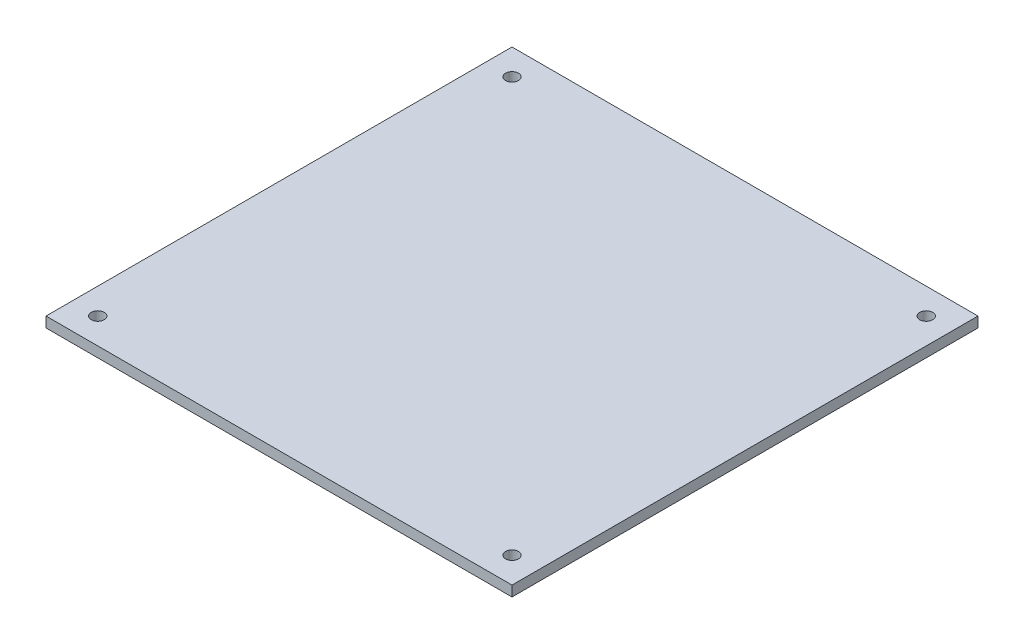
SolidWorks part; units mm, degrees
ref_plane "Front Plane" through (0, 0, 0) normal (0, 0, 1) x (1, 0, 0)
ref_plane "Top Plane" through (0, 0, 0) normal (0, 1, 0) x (1, 0, 0)
ref_plane "Right Plane" through (0, 0, 0) normal (1, 0, 0) x (0, 0, -1)
sketch "Sketch1" plane through (0, 0, 0) normal (0, 1, 0) x (1, 0, 0)
  line L1 (-45, -45) -> (45, -45)
  line L2 (-45, -45) -> (-45, 45)
  line L3 (-45, 45) -> (45, 45)
  line L4 (45, -45) -> (45, 45)
  line L5 (-45, -45) -> (45, 45) construction
  line L6 (-45, 45) -> (45, -45) construction
  point P0 (0, 0)
  dimension "D1" = 90
  dimension "D2" = 90
extrude "Boss-Extrude1" add sketch "Sketch1" along normal blind 2
sketch "Sketch2" plane through (0, 2, 0) normal (0, 1, 0) x (1, 0, 0)
  line L1 (-40, -40) -> (40, -40)
  line L2 (-40, -40) -> (-40, 40)
  line L3 (-40, 40) -> (40, 40)
  line L4 (40, -40) -> (40, 40)
  line L5 (-40, -40) -> (40, 40) construction
  line L6 (-40, 40) -> (40, -40) construction
  point P0 (0, 0)
  dimension "D1" = 80
  dimension "D2" = 80
hole_wizard "M3x0.5 Tapped Hole1" positions "Sketch3" profile "Sketch4" tap size "M3x0.5" standard "ANSI Metric" end condition through all
sketch "Sketch3" plane through (0, 2, 0) normal (0, 1, 0) x (1, 0, 0)
  point P0 (-40, 40)
  point P3 (40, 40)
  point P6 (40, -40)
  point P9 (-40, -40)
sketch "Sketch4" plane through (-40, 2, -40) normal (1, 0, 0) x (0, 0, 1)
  line L0 (0, 0) -> (0, 2)
  line L1 (0, 2) -> (1.25, 2)
  line L2 (1.25, 2) -> (1.25, 0)
  line L5 (1.25, 0) -> (0, 0)
  line L11 (0, -6.35) -> (0, 107.95) construction
  dimension "Thru Tap Drill Dia." = 2.5
  dimension "Thru Tap Drill Depth" = 2
cosmetic thread "Hole Thread1" parameters "D2"=3
cosmetic thread "Hole Thread2" parameters "D2"=3
cosmetic thread "Hole Thread3" parameters "D2"=3
cosmetic thread "Hole Thread4" parameters "D2"=3
